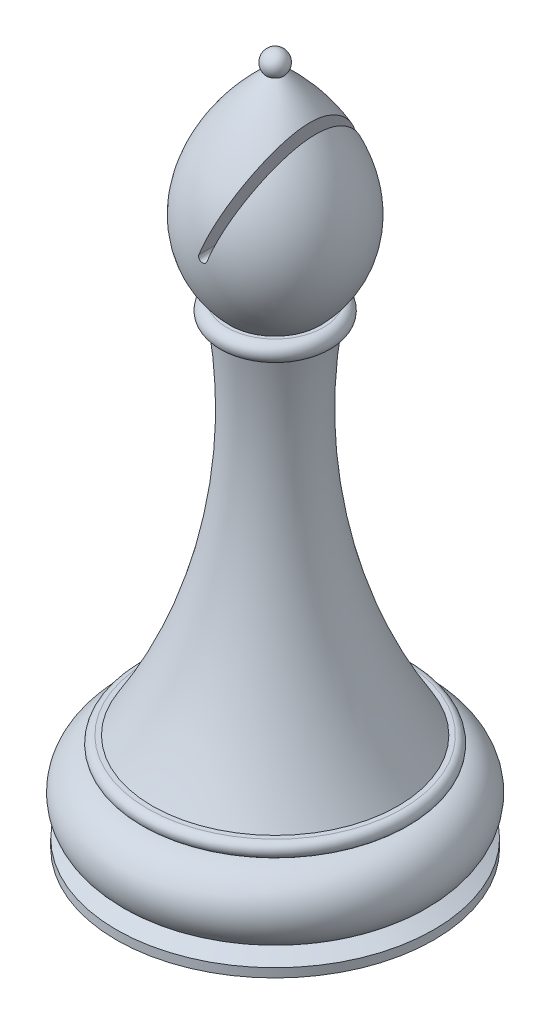
SolidWorks part; units mm, degrees
ref_plane "Front Plane" through (0, 0, 0) normal (0, 0, 1) x (1, 0, 0)
ref_plane "Top Plane" through (0, 0, 0) normal (0, 1, 0) x (1, 0, 0)
ref_plane "Right Plane" through (0, 0, 0) normal (1, 0, 0) x (0, 0, -1)
sketch "Sketch1" plane through (0, 0, 0) normal (0, 0, 1) x (1, 0, 0)
  line L0 (0, 0) -> (0, -19.2438) construction
  line L1 (0, 0) -> (12.5016, 0)
  line L2 (12.4781, -1.4284) -> (12.4781, -1.4347)
  line L3 (0, -9.6219) -> (15.5627, -9.6219)
  line L4 (15.5627, -9.6219) -> (15.5627, -8.7515)
  line L5 (15.5627, -8.7515) -> (13.8939, -7.9606)
  line L6 (0, 0) -> (0, -9.6219)
  line L7 (0, -9.6219) -> (0, 57.1409) construction
  line L8 (4.3896, 36.9784) -> (4.7294, 36.9784)
  line L9 (0, 57.1409) -> (0, -9.6219)
  line L10 (0, 59.8009) -> (0, 57.1409) construction
  line L11 (0, 58.274) -> (0, 57.1409)
  arc A0 (12.5016, 0) -> (12.4781, -1.4284) centre (12.5016, -0.7144) cw
  arc A1 (13.8939, -7.9606) -> (12.4781, -1.4347) centre (12.4226, -4.8633) ccw
  arc A2 (4.7294, 36.9784) -> (4.6574, 35.1839) centre (4.7294, 36.0798) cw
  arc A3 (4.6574, 35.1839) -> (12.0459, 0) centre (56.7127, 27.7477) ccw
  arc A4 (0.7216, 56.2672) -> (0, 58.274) centre (0, 57.1409) ccw
  spline S0 degree 3 poles (0, 57.1409) (8.6117, 49.7983) (9.3824, 41.9728) (4.3896, 36.9784) knots 0 0 0 0 0.785114 0.785114 0.785114 0.785114
  point P22 (12.0459, 0)
  dimension "D1" = 0.0064
  dimension "D4" = 0.7144
  dimension "D3" = 3.429
  dimension "D2" = 12.5016
  dimension "D5" = 9.6219
revolve "Revolve2" add sketch "Sketch1" angle 360 about L0
sketch "Sketch2" plane through (0, 0, 0) normal (0, 0, 1) x (1, 0, 0)
  line L6 (3.4183, 53.7382) -> (0, 44.5459)
  line L8 (0.7339, 44.273) -> (3.9913, 53.0324)
  arc A0 (0, 44.5459) -> (0.7339, 44.273) centre (0.367, 44.4095) ccw
  spline S1 degree 3 poles (-179.9621, 1998.502) (-659.1427, -1689.9106) (1321.666, 1388.1768) (-1785.5408, -808.5376) knots -6.111741 -6.111741 -6.111741 -6.111741 5.957924 5.957924 5.957924 5.957924 only from (4.3896, 36.9784) to (0.85, 56.3916) construction
  spline S3 degree 3 poles (3.9913, 53.0324) (3.8078, 53.2676) (3.6169, 53.5029) (3.4183, 53.7382) knots 0.639701 0.639701 0.639701 0.639701 0.664625 0.664625 0.664625 0.664625
extrude "Cut-Extrude2" cut sketch "Sketch2" against normal through all both and the other way through all
